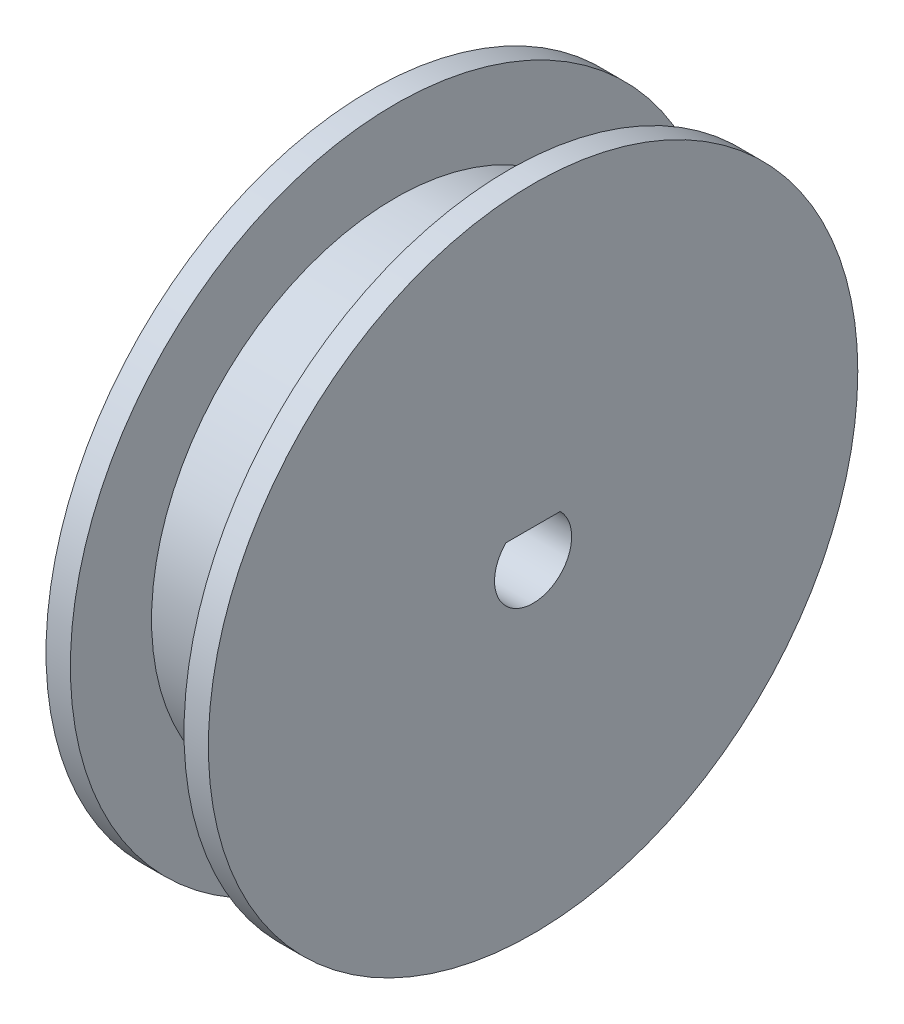
SolidWorks part; units mm, degrees
material "6061 Alloy"
ref_plane "Front Plane" through (0, 0, 0) normal (0, 0, 1) x (1, 0, 0)
ref_plane "Top Plane" through (0, 0, 0) normal (0, 1, 0) x (1, 0, 0)
ref_plane "Right Plane" through (0, 0, 0) normal (1, 0, 0) x (0, 0, -1)
sketch "Sketch1" plane through (0, 0, 0) normal (0, 0, 1) x (1, 0, 0)
  line L0 (-5, 0) -> (-5, 20)
  line L1 (-5, 20) -> (-3.5, 20)
  line L2 (-3.5, 20) -> (-3.5, 15)
  line L3 (-3.5, 15) -> (3.5, 15)
  line L4 (3.5, 15) -> (3.5, 20)
  line L5 (3.5, 20) -> (5, 20)
  line L6 (5, 20) -> (5, 0)
  line L7 (5, 0) -> (-5, 0)
  dimension "D1" = 10
  dimension "D2" = 1.5
  dimension "D3" = 1.5
  dimension "D4" = 15
  dimension "D5" = 20
revolve "Revolve1" add sketch "Sketch1" angle 360 about L7
sketch "Sketch2" plane through (5, 0, 0) normal (1, 0, 0) x (0, 0, -1)
  line L0 (-1.6695, 1.6891) -> (1.6695, 1.6891)
  circle A0 centre (0, 0) radius 2.3749
  dimension "D1" = 4.7498
  dimension "D2" = 3.3389
extrude "Cut-Extrude1" cut sketch "Sketch2" against normal through all contours L0 A0
